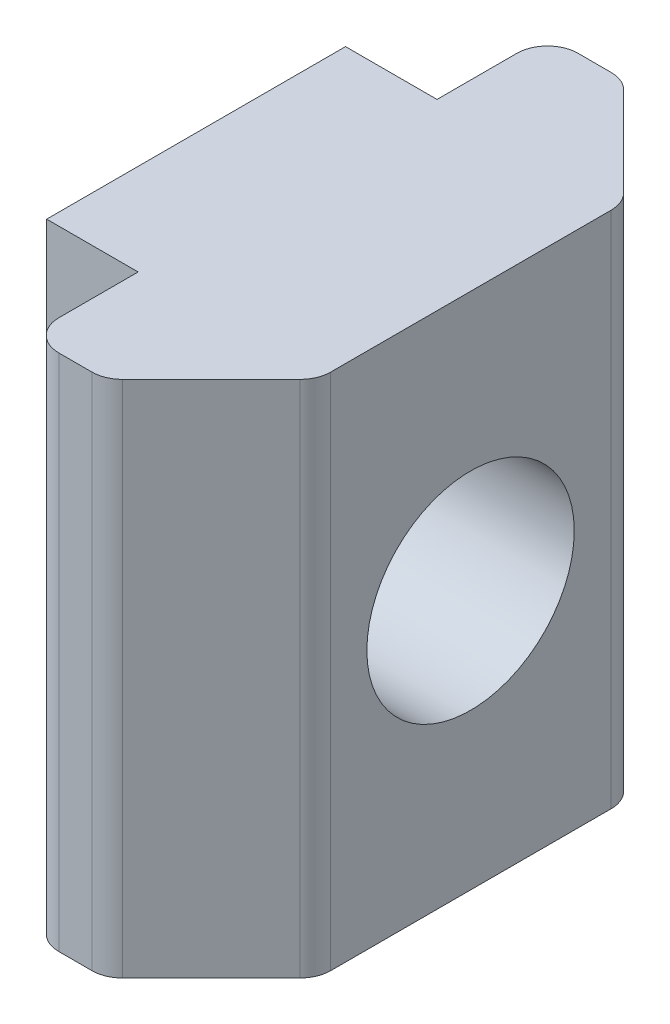
SolidWorks part; units mm, degrees
ref_plane "Front Plane" through (0, 0, 0) normal (0, 0, 1) x (1, 0, 0)
ref_plane "Top Plane" through (0, 0, 0) normal (0, 1, 0) x (1, 0, 0)
ref_plane "Right Plane" through (0, 0, 0) normal (1, 0, 0) x (0, 0, -1)
sketch "Sketch1" plane through (0, 0, 0) normal (0, 1, 0) x (1, 0, 0)
  line L4 (10.2143, -18.2665) -> (13.1285, -15.3523)
  line L5 (9.5072, -18.5594) -> (8.4214, -18.5594)
  line L6 (7.4214, -14.9594) -> (4.4214, -14.9594)
  line L7 (7.4214, -5.1594) -> (4.4214, -5.1594)
  line L8 (4.4214, -14.9594) -> (4.4214, -5.1594)
  line L9 (13.4214, -14.6452) -> (13.4214, -5.4516)
  line L10 (7.4214, -17.5594) -> (7.4214, -14.9594)
  line L11 (10.2143, -1.8303) -> (13.1285, -4.7445)
  line L12 (7.4214, -5.1594) -> (7.4214, -2.5374)
  line L13 (9.5072, -1.5374) -> (8.4214, -1.5374)
  arc A0 (7.4214, -17.5594) -> (8.4214, -18.5594) centre (8.4214, -17.5594) ccw
  arc A1 (9.5072, -18.5594) -> (10.2143, -18.2665) centre (9.5072, -17.5594) ccw
  arc A2 (10.2143, -1.8303) -> (9.5072, -1.5374) centre (9.5072, -2.5374) ccw
  arc A3 (8.4214, -1.5374) -> (7.4214, -2.5374) centre (8.4214, -2.5374) ccw
  arc A4 (13.1285, -15.3523) -> (13.4214, -14.6452) centre (12.4214, -14.6452) ccw
  arc A5 (13.4214, -5.4516) -> (13.1285, -4.7445) centre (12.4214, -5.4516) ccw
extrude "Boss-Extrude1" add sketch "Sketch1" along normal blind 17
sketch "Sketch2" plane through (4.4214, 0, 0) normal (-1, 0, 0) x (0, 0, 1)
  line L0 (10.0594, 17) -> (10.0594, 0) construction
  line L1 (5.1594, 17) -> (14.9594, 17) construction
  line L2 (5.1594, 0) -> (14.9594, 0) construction
  line L3 (5.1594, 8.5) -> (14.9594, 8.5) construction
  line L4 (5.1594, 17) -> (5.1594, 0) construction
  line L5 (14.9594, 17) -> (14.9594, 0) construction
  point P12 (10.0594, 8.5)
hole_wizard "M5 Tapped Hole1" positions "3DSketch1" profile "Sketch3" tap size "M5" standard "ISO"
sketch3d "3DSketch1"
  point P0 (4.4214, 8.5, 10.0594)
sketch "Sketch3" plane through (4.4214, 8.5, 10.0594) normal (0, 1, 0) x (0, 0, 1)
  line L0 (0, 0) -> (0, 9)
  line L1 (0, 9) -> (2.1, 9)
  line L2 (2.1, 9) -> (2.1, 0)
  line L5 (2.1, 0) -> (0, 0)
  line L11 (0, -6.35) -> (0, 107.95) construction
  dimension "Thread Major Dia." = 4.2
  dimension "Thru Tap Drill Depth" = 9
hole_wizard "M4 Tapped Hole1" positions "Sketch5" profile "Sketch4" tap size "M4" standard "ISO"
sketch "Sketch5" plane through (4.4214, 0, 0) normal (-1, 0, 0) x (0, 0, 1)
  point P0 (10.0594, 8.5)
sketch "Sketch4" plane through (4.4214, 8.5, 10.0594) normal (0, 1, 0) x (0, 0, 1)
  line L0 (0, 0) -> (0, 9)
  line L1 (0, 9) -> (1.65, 9)
  line L2 (1.65, 9) -> (1.65, 0)
  line L5 (1.65, 0) -> (0, 0)
  line L11 (0, -6.35) -> (0, 107.95) construction
  dimension "Thread Major Dia." = 3.3
  dimension "Thru Tap Drill Depth" = 9
hole_wizard "M6 Tapped Hole1" positions "3DSketch2" profile "Sketch6" tap size "M6" standard "ISO"
sketch3d "3DSketch2"
  point P0 (4.4214, 8.5, 10.0594)
sketch "Sketch6" plane through (4.4214, 8.5, 10.0594) normal (0, 1, 0) x (0, 0, 1)
  line L0 (0, 0) -> (0, 9)
  line L1 (0, 9) -> (2.5, 9)
  line L2 (2.5, 9) -> (2.5, 0)
  line L5 (2.5, 0) -> (0, 0)
  line L11 (0, -6.35) -> (0, 107.95) construction
  dimension "Thread Major Dia." = 5
  dimension "Thru Tap Drill Depth" = 9
hole_wizard "M8 Tapped Hole1" positions "3DSketch3" profile "Sketch7" tap size "M8" standard "ISO" end condition through all
sketch3d "3DSketch3"
  point P0 (4.4214, 8.5, 10.0594)
sketch "Sketch7" plane through (4.4214, 8.5, 10.0594) normal (0, 1, 0) x (0, 0, 1)
  line L0 (0, 0) -> (0, 9)
  line L1 (0, 9) -> (3.4, 9)
  line L2 (3.4, 9) -> (3.4, 0)
  line L5 (3.4, 0) -> (0, 0)
  line L11 (0, -6.35) -> (0, 107.95) construction
  dimension "Thread Major Dia." = 6.8
  dimension "Thru Tap Drill Depth" = 9
